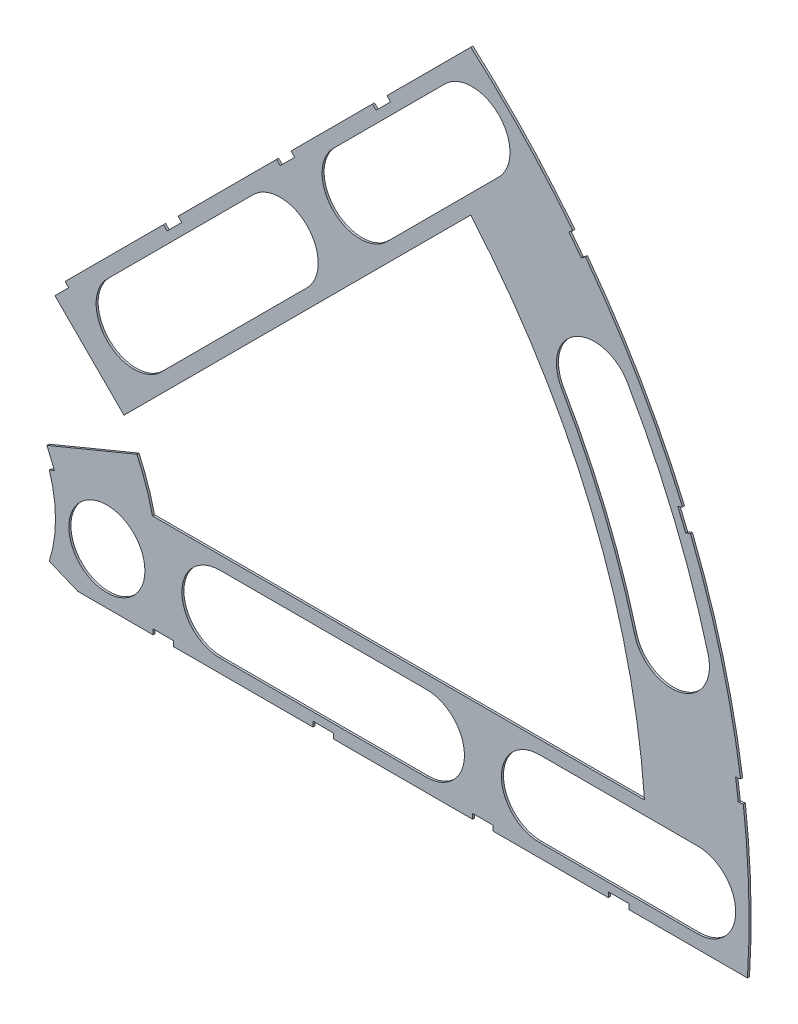
SolidWorks part; units mm, degrees
material "PTFE (general)"
ref_plane "Front Plane" through (0, 0, 0) normal (0, 0, 1) x (1, 0, 0)
ref_plane "Top Plane" through (0, 0, 0) normal (0, 1, 0) x (1, 0, 0)
ref_plane "Right Plane" through (0, 0, 0) normal (1, 0, 0) x (0, 0, -1)
sketch "Sketch1" plane through (0, 0, 0) normal (0, 0, 1) x (1, 0, 0)
  line L0 (0, 0) -> (320.3893, 0) construction
  line L1 (0, 0) -> (155.5285, 155.5285) construction
  line L2 (67.2115, 76.1917) -> (8.6967, 17.6769)
  line L3 (8.6967, 17.6769) -> (7.229, 14.1336)
  line L4 (101.4014, -6.35) -> (18.6489, -6.35)
  line L5 (15.1056, -4.8823) -> (18.6489, -6.35)
  line L6 (88.6729, 6.35) -> (27.8605, 6.35)
  line L9 (67.1914, 58.2111) -> (24.1905, 15.2102)
  line L10 (0, 0) -> (40.4486, 97.6516) construction
  line L11 (0, 0) -> (123.4567, -51.1374) construction
  line L18 (8.6967, 17.6769) -> (13.294, 8.6183) construction
  line L19 (18.6489, -6.35) -> (15.4943, 3.3063) construction
  line L20 (27.8605, 6.35) -> (27.7442, 6.7059) construction
  line L21 (24.1905, 15.2102) -> (24.3599, 14.8764) construction
  arc A0 (7.229, 14.1336) -> (15.1056, -4.8823) centre (0, 0) cw
  arc A1 (67.2115, 76.1917) -> (101.4014, -6.35) centre (0, 0) cw
  arc A2 (24.1905, 15.2102) -> (27.8605, 6.35) centre (0, 0) cw
  arc A3 (67.1914, 58.2111) -> (88.6729, 6.35) centre (0, 0) cw
  arc A8 (13.294, 8.6183) -> (15.4943, 3.3063) centre (0, 0) cw construction
  arc A9 (24.3599, 14.8764) -> (27.7442, 6.7059) centre (0, 0) cw construction
  dimension "D1" = 45
  dimension "D3" = 6.35
  dimension "D4" = 15.875
  dimension "D7" = 22.5
  dimension "D8" = 101.6
  dimension "D11" = 12.7
  dimension "D12" = 12.7
  dimension "D2" = 6.35
  dimension "D5" = 67.5
  dimension "D9" = 1.27
  dimension "D10" = 1.27
  dimension "D6" = 12.7
extrude "Boss-Extrude1" add sketch "Sketch1" along normal blind 0.254
sketch "Sketch2" plane through (0, 0, 0.254) normal (0, 0, 1) x (1, 0, 0)
  line L0 (0, 0) -> (101.6, 0) construction
  line L1 (0, 0) -> (71.842, 71.842) construction
  line L3 (0, 0) -> (22.225, 0) construction
  line L4 (0, 0) -> (15.7154, 15.7154) construction
  line L5 (0, 0) -> (95.25, 0) construction
  line L6 (0, 0) -> (92.0044, 24.6525) construction
  arc A0 (101.4014, -6.35) -> (67.2115, 76.1917) centre (0, 0) ccw construction
  circle A1 centre (22.225, 0) radius 4.699
  arc A2 (15.1056, -4.8823) -> (7.229, 14.1336) centre (0, 0) ccw construction
  circle A3 centre (36.195, 0) radius 4.699
  circle A4 centre (61.722, 0) radius 4.699
  circle A5 centre (75.692, 0) radius 4.699
  circle A6 centre (95.25, 0) radius 4.699
  circle A7 centre (15.7154, 15.7154) radius 4.699
  circle A8 centre (25.5937, 25.5937) radius 4.699
  circle A9 centre (43.644, 43.644) radius 4.699
  circle A10 centre (53.5223, 53.5223) radius 4.699
  circle A11 centre (92.0044, 24.6525) radius 4.699
  circle A12 centre (82.4889, 47.625) radius 4.699
  circle A13 centre (67.3519, 67.3519) radius 4.699
  dimension "D3" = 9.398
  dimension "D1" = 45
  dimension "D2" = 6.35
  dimension "D4" = 6.35
  dimension "D5" = 13.97
  dimension "D7" = 13.97
  dimension "D8" = 19.558
  dimension "D9" = 45
  dimension "D10" = 15
  dimension "D11" = 25.527
  dimension "D6" = 2
extrude "Cut-Extrude1" cut sketch "Sketch2" against normal through all
sketch "Sketch3" plane through (0, 0, 0.254) normal (0, 0, 1) x (1, 0, 0)
  line L0 (15.2664, 24.2467) -> (17.0625, 26.0427)
  line L1 (15.2664, 24.2467) -> (15.7154, 23.7977)
  line L2 (17.0625, 26.0427) -> (17.5115, 25.5937)
  line L3 (15.7154, 23.7977) -> (17.5115, 25.5937)
  line L4 (67.2115, 76.1917) -> (8.6967, 17.6769) construction
  line L5 (44.9911, 53.9713) -> (43.195, 52.1753)
  line L6 (44.9911, 53.9713) -> (45.4401, 53.5223)
  line L7 (43.195, 52.1753) -> (43.644, 51.7263)
  line L8 (45.4401, 53.5223) -> (43.644, 51.7263)
  line L9 (27.94, -6.35) -> (30.48, -6.35)
  line L10 (27.94, -6.35) -> (27.94, -5.715)
  line L11 (30.48, -6.35) -> (30.48, -5.715)
  line L12 (27.94, -5.715) -> (30.48, -5.715)
  line L13 (18.6489, -6.35) -> (101.4014, -6.35) construction
  line L14 (67.437, -6.35) -> (69.977, -6.35)
  line L15 (67.437, -6.35) -> (67.437, -5.715)
  line L16 (69.977, -6.35) -> (69.977, -5.715)
  line L17 (67.437, -5.715) -> (69.977, -5.715)
  line L18 (29.2307, 38.211) -> (31.0268, 40.007)
  line L19 (29.2307, 38.211) -> (29.6797, 37.762)
  line L20 (31.0268, 40.007) -> (31.4758, 39.558)
  line L21 (29.6797, 37.762) -> (31.4758, 39.558)
  line L22 (56.845, 65.8253) -> (55.049, 64.0292)
  line L23 (56.845, 65.8253) -> (57.294, 65.3763)
  line L24 (55.049, 64.0292) -> (55.498, 63.5802)
  line L25 (57.294, 65.3763) -> (55.498, 63.5802)
  line L26 (47.6885, -6.35) -> (50.2285, -6.35)
  line L27 (47.6885, -6.35) -> (47.6885, -5.715)
  line L28 (50.2285, -6.35) -> (50.2285, -5.715)
  line L29 (47.6885, -5.715) -> (50.2285, -5.715)
  line L30 (84.201, -6.35) -> (86.741, -6.35)
  line L31 (84.201, -6.35) -> (84.201, -5.715)
  line L32 (86.741, -6.35) -> (86.741, -5.715)
  line L33 (84.201, -5.715) -> (86.741, -5.715)
  line L34 (0, 0) -> (100.7308, 13.2615) construction
  line L35 (0, 0) -> (93.8662, 38.8806) construction
  line L36 (0, 0) -> (80.6047, 61.8502) construction
  line L37 (0, 0) -> (101.6, 0) construction
  line L38 (99.9355, 14.4377) -> (100.267, 11.9194)
  line L39 (99.9355, 14.4377) -> (101.1946, 14.6035)
  line L40 (100.267, 11.9194) -> (101.5261, 12.0852)
  line L41 (101.1946, 14.6035) -> (101.5261, 12.0852)
  line L42 (99.9355, 14.4377) -> (101.5261, 12.0852) construction
  line L43 (100.267, 11.9194) -> (101.1946, 14.6035) construction
  line L44 (93.7655, 37.4643) -> (94.9388, 37.9503)
  line L45 (93.7655, 37.4643) -> (92.7935, 39.811)
  line L46 (94.9388, 37.9503) -> (93.9668, 40.297)
  line L47 (92.7935, 39.811) -> (93.9668, 40.297)
  line L48 (93.7655, 37.4643) -> (93.9668, 40.297) construction
  line L49 (94.9388, 37.9503) -> (92.7935, 39.811) construction
  line L50 (79.3278, 62.4712) -> (80.874, 60.456)
  line L51 (79.3278, 62.4712) -> (80.3354, 63.2443)
  line L52 (80.874, 60.456) -> (81.8816, 61.2292)
  line L53 (80.3354, 63.2443) -> (81.8816, 61.2292)
  line L54 (79.3278, 62.4712) -> (81.8816, 61.2292) construction
  line L55 (80.874, 60.456) -> (80.3354, 63.2443) construction
  line L56 (13.5939, 7.0054) -> (14.5659, 4.6588)
  line L57 (13.5939, 7.0054) -> (14.7672, 7.4914)
  line L58 (14.5659, 4.6588) -> (15.7393, 5.1448)
  line L59 (14.7672, 7.4914) -> (15.7393, 5.1448)
  line L60 (13.5939, 7.0054) -> (15.7393, 5.1448) construction
  line L61 (14.5659, 4.6588) -> (14.7672, 7.4914) construction
  circle A0 centre (15.7154, 15.7154) radius 4.699 construction
  circle A1 centre (43.644, 43.644) radius 4.699 construction
  circle A2 centre (22.225, 0) radius 4.699 construction
  circle A3 centre (61.722, 0) radius 4.699 construction
  arc A4 (101.4014, -6.35) -> (67.2115, 76.1917) centre (0, 0) ccw construction
  arc A9 (15.1056, -4.8823) -> (7.229, 14.1336) centre (0, 0) ccw construction
  circle A10 centre (36.195, 0) radius 4.699 construction
  circle A11 centre (75.692, 0) radius 4.699 construction
  circle A12 centre (25.5937, 25.5937) radius 4.699 construction
  circle A13 centre (53.5223, 53.5223) radius 4.699 construction
  point P75 (14.6666, 6.0751)
  dimension "D2" = 5.715
  dimension "D3" = 2.54
  dimension "D6" = 5.715
  dimension "D8" = 0.635
  dimension "D9" = 5.715
  dimension "D12" = 5.715
  dimension "D4" = 7.5
  dimension "D5" = 22.5
  dimension "D7" = 37.5
  dimension "D10" = 90
  dimension "D11" = 1.27
  dimension "D14" = 0.635
  dimension "D15" = 90
  dimension "D18" = 0.635
  dimension "D19" = 90
  dimension "D22" = 0.635
  dimension "D20" = 1.27
  dimension "D17" = 0.635
  dimension "D21" = 11.4935
  dimension "D13" = 8.509
  dimension "D16" = 11.4935
  dimension "D23" = 8.509
extrude "Cut-Extrude2" cut sketch "Sketch3" against normal through all
sketch "Sketch5" plane through (0, 0, 0.254) normal (0, 0, 1) x (1, 0, 0)
  line L0 (8.419, 4.7244) -> (27.1922, 12.5005)
  line L1 (17.5115, 25.5937) -> (17.0625, 26.0427) construction
  line L2 (15.1056, 4.8823) -> (15.7393, 5.1448) construction
  line L4 (27.1922, 12.5005) -> (12.8238, 26.869)
  line L7 (15.7154, 23.7977) -> (17.5115, 25.5937) construction
  line L8 (12.8238, 26.869) -> (-0.4509, 13.5943)
  line L9 (-0.4509, 13.5943) -> (8.419, 4.7244)
  dimension "D1" = 2.413
  dimension "D2" = 2.413
  dimension "D3" = 90
  dimension "D4" = 20.32
  dimension "D5" = 90
  dimension "D6" = 20.32
  dimension "D7" = 90
sketch "Sketch6" plane through (0, 0, 0.254) normal (0, 0, 1) x (1, 0, 0)
  line L0 (0, 0) -> (101.6, 0) construction
  line L1 (0, 0) -> (71.842, 71.842) construction
  line L2 (0, 0) -> (87.9882, 50.8) construction
  line L3 (0, 0) -> (98.1381, 26.296) construction
  line L4 (25.5937, 25.5937) -> (43.644, 43.644) construction
  line L5 (22.271, 28.9164) -> (40.3213, 46.9667)
  line L6 (28.9164, 22.271) -> (46.9667, 40.3213)
  line L7 (53.5223, 53.5223) -> (67.3519, 67.3519) construction
  line L8 (50.1996, 56.845) -> (64.0292, 70.6746)
  line L9 (56.845, 50.1996) -> (70.6746, 64.0292)
  line L10 (61.722, 0) -> (36.195, 0) construction
  line L11 (61.722, -4.699) -> (36.195, -4.699)
  line L12 (61.722, 4.699) -> (36.195, 4.699)
  line L13 (95.25, 0) -> (75.692, 0) construction
  line L14 (95.25, -4.699) -> (75.692, -4.699)
  line L15 (95.25, 4.699) -> (75.692, 4.699)
  arc A0 (79.8253, 62.8529) -> (67.2115, 76.1917) centre (0, 0) ccw construction
  circle A1 centre (67.3519, 67.3519) radius 4.699 construction
  circle A2 centre (43.644, 43.644) radius 4.699 construction
  arc A5 (101.4014, -6.35) -> (100.8887, 12.0013) centre (0, 0) ccw construction
  arc A7 (93.3728, 40.0509) -> (81.3715, 60.8378) centre (0, 0) ccw construction
  arc A8 (100.5572, 14.5196) -> (94.3448, 37.7043) centre (0, 0) ccw construction
  arc A9 (82.4889, 47.625) -> (92.0044, 24.6525) centre (0, 0) cw construction
  arc A10 (96.5433, 25.8687) -> (86.5584, 49.9745) centre (0, 0) ccw
  arc A11 (87.4655, 23.4363) -> (78.4195, 45.2755) centre (0, 0) ccw
  arc A12 (87.4655, 23.4363) -> (96.5433, 25.8687) centre (92.0044, 24.6525) ccw
  arc A13 (86.5584, 49.9745) -> (78.4195, 45.2755) centre (82.4889, 47.625) ccw
  arc A14 (22.271, 28.9164) -> (28.9164, 22.271) centre (25.5937, 25.5937) ccw
  arc A15 (46.9667, 40.3213) -> (40.3213, 46.9667) centre (43.644, 43.644) ccw
  arc A16 (50.1996, 56.845) -> (56.845, 50.1996) centre (53.5223, 53.5223) ccw
  arc A17 (70.6746, 64.0292) -> (64.0292, 70.6746) centre (67.3519, 67.3519) ccw
  arc A18 (61.722, -4.699) -> (61.722, 4.699) centre (61.722, 0) ccw
  arc A19 (36.195, 4.699) -> (36.195, -4.699) centre (36.195, 0) ccw
  arc A20 (95.25, -4.699) -> (95.25, 4.699) centre (95.25, 0) ccw
  arc A21 (75.692, 4.699) -> (75.692, -4.699) centre (75.692, 0) ccw
  point P12 (87.9995, 36.4506)
  point P43 (34.6189, 34.6189)
  point P48 (60.4371, 60.4371)
  point P59 (48.9585, 0)
  point P70 (85.471, 0)
  dimension "D4" = 9.398
  dimension "D1" = 45
  dimension "D2" = 9.398
  dimension "D3" = 9.398
extrude "Cut-Extrude4" cut sketch "Sketch6" against normal through all
extrude "Cut-Extrude5" cut sketch "Sketch5" against normal through all
equation "\"cSep\"= 1.005"
equation "\"D11@Sketch2\"=\"cSep\""
equation "\"cSep2\"= \"D8@Sketch2\""
equation "\"D21@Sketch3\"=\"cSep\"/2-.05"
equation "\"D13@Sketch3\"=\"cSep2\"/2-.05"
equation "\"D16@Sketch3\"=\"cSep\"/2-.05"
equation "\"D23@Sketch3\"=\"cSep2\"/2-.05"
